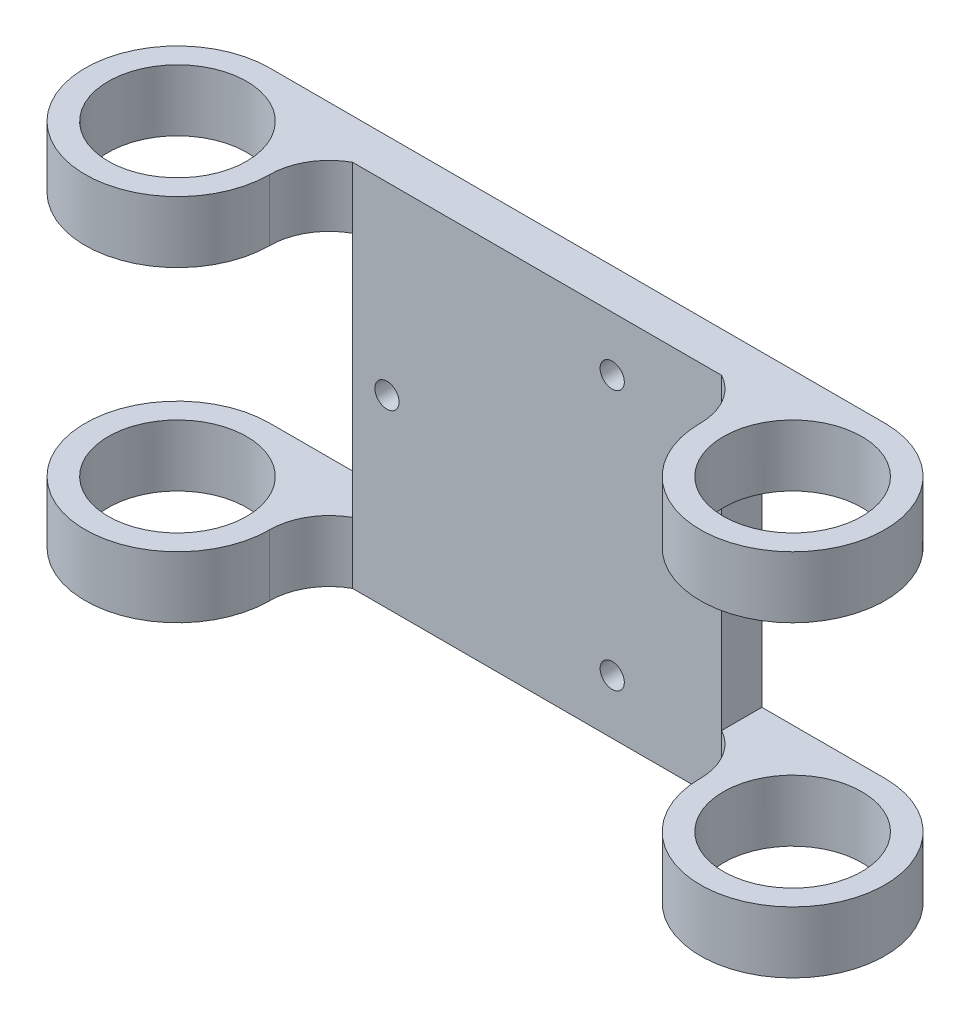
SolidWorks part; units mm, degrees
ref_plane "Front Plane" through (0, 0, 0) normal (0, 0, 1) x (1, 0, 0)
ref_plane "Top Plane" through (0, 0, 0) normal (0, 1, 0) x (1, 0, 0)
ref_plane "Right Plane" through (0, 0, 0) normal (1, 0, 0) x (0, 0, -1)
sketch "Sketch1" plane through (0, 0, 0) normal (0, 1, 0) x (1, 0, 0)
  line L0 (63.5, 0) -> (-63.5, 0)
  line L1 (-63.5, 0) -> (-63.5, -38.1) construction
  line L2 (-63.5, -38.1) -> (63.5, -38.1) construction
  line L3 (63.5, -38.1) -> (63.5, 0) construction
  line L4 (0, 0) -> (0, -38.1) construction
  line L6 (-77.7875, -19.05) -> (77.7875, -19.05) construction
  line L7 (38.1, -8.3) -> (-38.1, -8.3)
  arc A0 (-63.5, 0) -> (-44.45, -19.05) centre (-63.5, -19.05) ccw
  arc A1 (63.5, 0) -> (44.45, -19.05) centre (63.5, -19.05) cw
  circle A4 centre (-63.5, -19.05) radius 14.2875
  circle A5 centre (63.5, -19.05) radius 14.2875
  arc A8 (-44.45, -19.05) -> (-38.1, -8.3) centre (-32.1756, -19.05) cw
  arc A9 (44.45, -19.05) -> (38.1, -8.3) centre (32.1756, -19.05) ccw
  point P4 (0, 0)
  point P12 (0, -8.3)
  point P26 (0, -8.3)
  dimension "D4" = 28.575
  dimension "D1" = 38.1
  dimension "D2" = 127
  dimension "D3" = 76.2
  dimension "D5" = 8.3
extrude "Boss-Extrude1" add sketch "Sketch1" along normal blind 76.2
sketch "Sketch2" plane through (0, 0, 0) normal (0, 0, -1) x (-1, 0, 0)
  line L0 (0, 0) -> (0, 76.2) construction
  line L1 (-63.5, 76.2) -> (63.5, 76.2) construction
  line L2 (38.1, 38.1) -> (-38.1, 38.1) construction
  line L3 (-38.1, 12.7) -> (-38.1, 63.5)
  line L4 (-38.1, 63.5) -> (-38.1, 12.7)
  line L5 (-38.1, 63.5) -> (-168.0908, 63.5)
  line L6 (-38.1, 12.7) -> (-168.0908, 12.7)
  line L7 (-168.0908, 63.5) -> (-168.0908, 12.7)
  line L8 (38.1, 12.7) -> (38.1, 63.5)
  line L9 (38.1, 63.5) -> (38.1, 12.7)
  line L10 (38.1, 63.5) -> (132.1995, 63.5)
  line L11 (38.1, 12.7) -> (132.1995, 12.7)
  line L12 (132.1995, 63.5) -> (132.1995, 12.7)
  line L14 (31.0002, 38.1) -> (-15.5001, 64.947) construction
  line L15 (-15.5001, 64.947) -> (-15.5001, 11.253) construction
  line L16 (-15.5001, 11.253) -> (31.0002, 38.1) construction
  circle A0 centre (0, 38.1) radius 15.5001 construction
  circle A1 centre (-15.5001, 64.947) radius 2.5
  circle A2 centre (31.0002, 38.1) radius 2.5
  circle A3 centre (-15.5001, 11.253) radius 2.5
  point P8 (0, 38.1)
  point P9 (0, 38.1)
  point P12 (-38.1, 38.1)
  point P17 (38.1, 38.1)
  line M10 (63.5, 0) -> (63.5, 76.2)
  line M12 (-63.5, 76.2) -> (-63.5, 0)
  dimension "D4" = 5
  dimension "D1" = 50.8
  dimension "D2" = 76.2
  dimension "D3" = 53.694
extrude "Cut-Extrude1" cut sketch "Sketch2" against normal through all both and the other way through all contours L6 L3 L5 M12 | L5 L7 L6 M12 | L8 L11 L10 M10 | L12 L10 L11 M10 | A1 | A3 | A2
